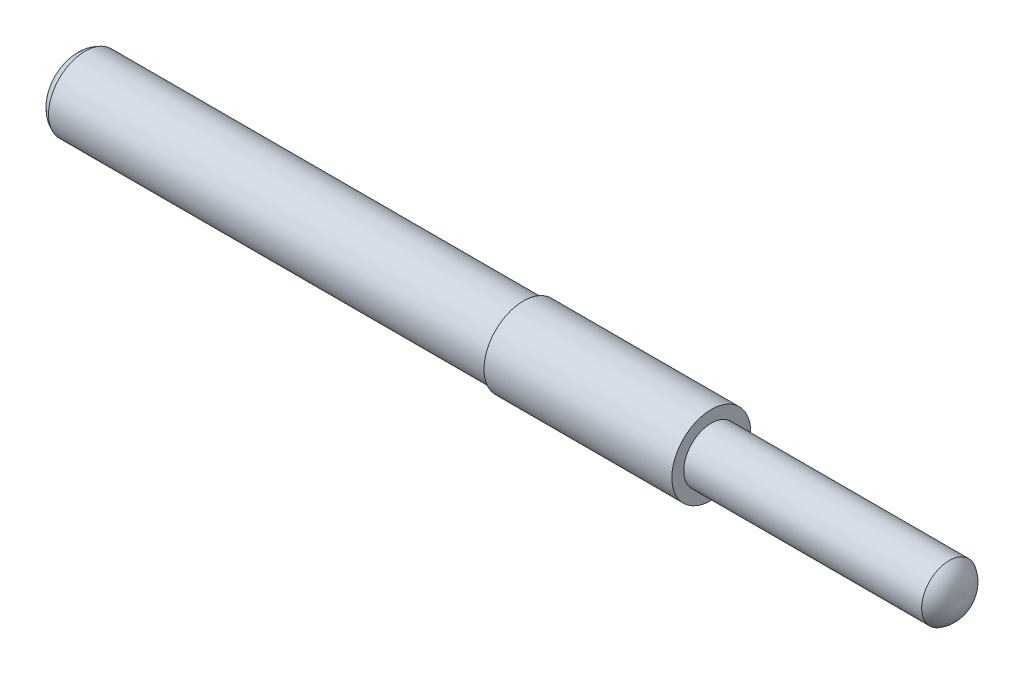
SolidWorks part; units mm, degrees
ref_plane "Front Plane" through (0, 0, 0) normal (0, 0, 1) x (1, 0, 0)
ref_plane "Top Plane" through (0, 0, 0) normal (0, 1, 0) x (1, 0, 0)
ref_plane "Right Plane" through (0, 0, 0) normal (1, 0, 0) x (0, 0, -1)
sketch "Sketch4" plane through (0, 0, 0) normal (0, 0, 1) x (1, 0, 0)
  line L0 (-50, 0) -> (50, 0)
  line L4 (30, 0) -> (30, -2.2)
  line L5 (30, -2.2) -> (49, -2.2)
  line L6 (30, 0) -> (30, -3.15)
  line L7 (30, -3.15) -> (15, -3.15)
  line L8 (15, -3.15) -> (15, 0)
  line L9 (15, 0) -> (15, -2.925)
  line L10 (15, -2.925) -> (-20, -2.925)
  line L11 (50, 0) -> (88.129, 0)
  arc A2 (49, -2.2) -> (50, 0) centre (47.9718, -0.4054) ccw
  arc A3 (-20, -2.925) -> (-20, 0) centre (-19.4698, -1.4625) cw
  point P3 (0, 0)
  dimension "D2" = 100
  dimension "D3" = 30
  dimension "D6" = 35
  dimension "D7" = 19
  dimension "D1" = 3.15
  dimension "D4" = 15
  dimension "D5" = 2.925
  dimension "D8" = 2.2
revolve "Revolve5" add sketch "Sketch4" angle 360 about L0
